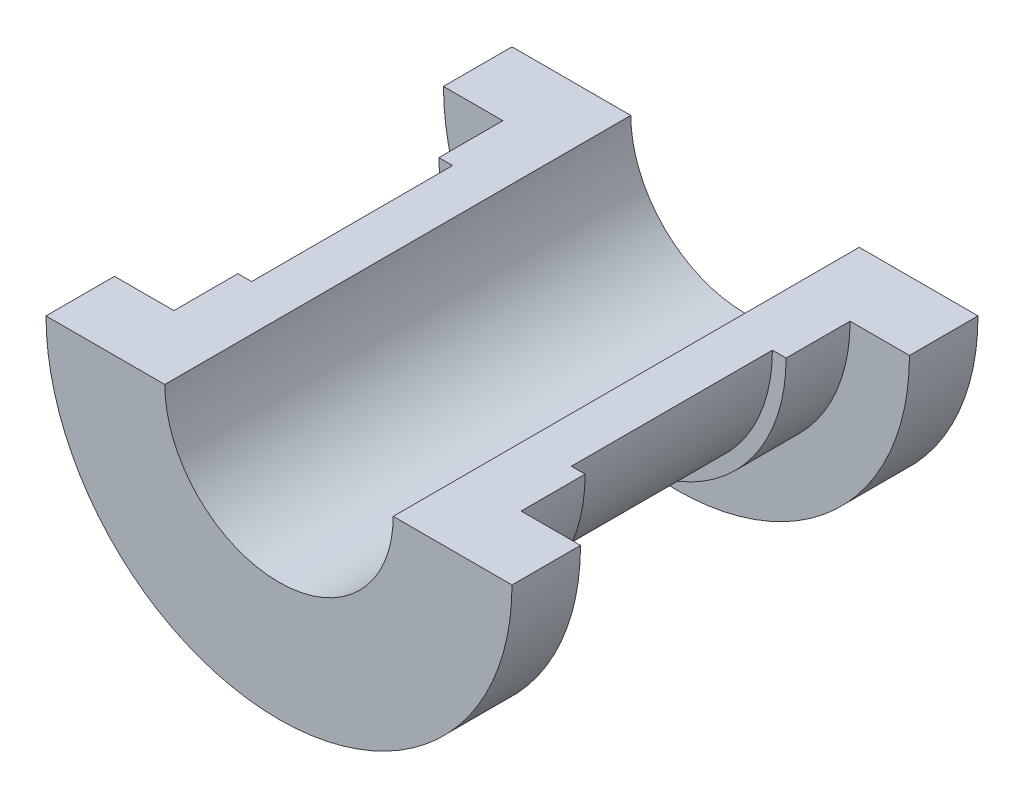
SolidWorks part; units mm, degrees
ref_plane "Front Plane" through (0, 0, 0) normal (0, 0, 1) x (1, 0, 0)
ref_plane "Top Plane" through (0, 0, 0) normal (0, 1, 0) x (1, 0, 0)
ref_plane "Right Plane" through (0, 0, 0) normal (1, 0, 0) x (0, 0, -1)
sketch "Sketch1" plane through (0, 0, 0) normal (0, 1, 0) x (1, 0, 0)
  line L0 (0, 0) -> (0, 67024.655) construction
  line L1 (0, 0) -> (67024.655, 0) construction
  line L2 (-25.5, 25.5) -> (-25.5, 18)
  line L3 (-25.5, 18) -> (-19, 18)
  line L4 (-19, 18) -> (-19, 11)
  line L5 (-19, 11) -> (-17.5, 11)
  line L6 (-17.5, 11) -> (-17.5, -11)
  line L7 (-25.5, 25.5) -> (-12.5, 25.5)
  line L8 (-12.5, 25.5) -> (-12.5, -25.5)
  line L9 (-19, -11) -> (-17.5, -11)
  line L10 (-25.5, -25.5) -> (-12.5, -25.5)
  line L11 (-19, -18) -> (-19, -11)
  line L12 (-25.5, -18) -> (-19, -18)
  line L13 (-25.5, -25.5) -> (-25.5, -18)
  point P15 (-17.5, 0)
  point P16 (-12.5, 0)
  dimension "D1" = 12.5
  dimension "D2" = 17.5
  dimension "D3" = 38
  dimension "D4" = 51
  dimension "D5" = 11
  dimension "D6" = 18
  dimension "D7" = 25.5
revolve "Revolve1" add sketch "Sketch1" angle 180 about L0
ref_plane "Plane1" through (0, -17.5, 0) normal (0, -1, 0) x (-1, 0, 0)
sketch "Sketch2" plane through (0, -17.5, 0) normal (0, -1, 0) x (-1, 0, 0)
  circle A0 centre (0, 0) radius 3
  dimension "D1" = 3
extrude "Boss-Extrude1" add sketch "Sketch2" along normal blind 6 separate body
